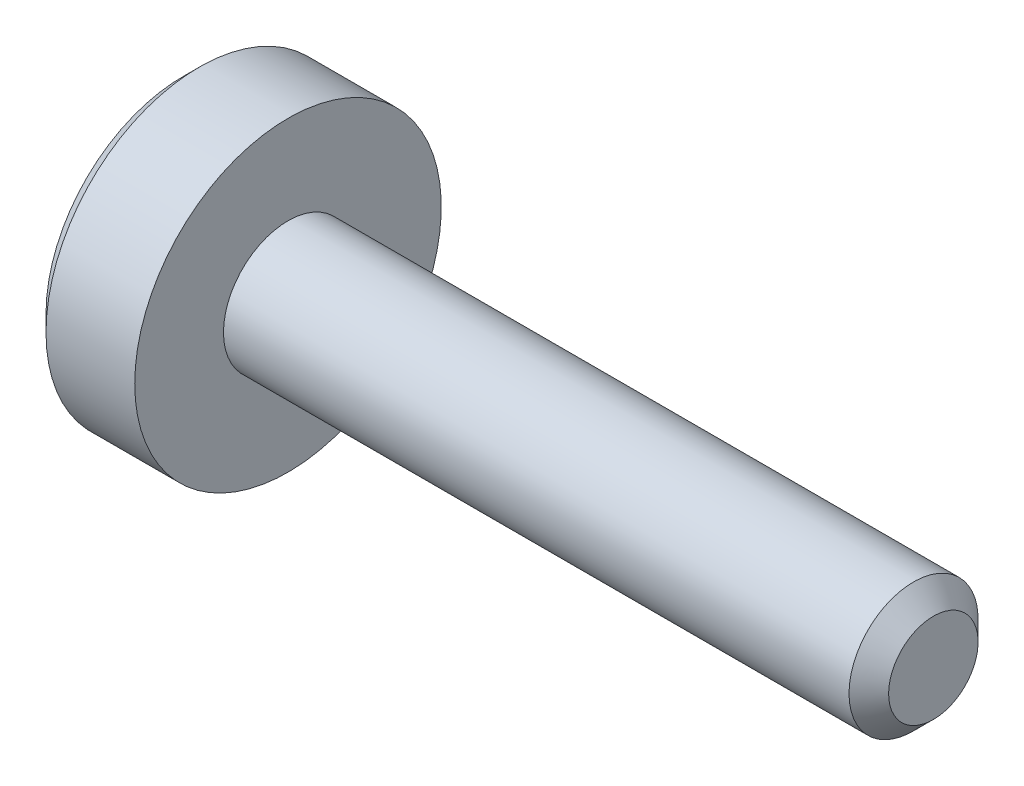
SolidWorks part; units mm, degrees
material "AISI 304"
ref_plane "正面" through (0, 0, 0) normal (0, 0, 1) x (1, 0, 0)
ref_plane "平面" through (0, 0, 0) normal (0, 1, 0) x (1, 0, 0)
ref_plane "右側面" through (0, 0, 0) normal (1, 0, 0) x (0, 0, -1)
ref_plane "Plane1" through (0, 0, 0) normal (0, 0, 1) x (1, 0, 0)
sketch "Sketch1" plane through (0, 0, 0) normal (0, 0, 1) x (1, 0, 0)
  line L0 (-1.3, 0) -> (-1.3, 1.7)
  line L1 (-1.3, 1.7) -> (-1.1, 1.9)
  line L2 (-1.1, 1.9) -> (0, 1.9)
  line L3 (0, 1.9) -> (0, 0.8)
  line L4 (0, 0.8) -> (7.7545, 0.8)
  line L5 (7.7545, 0.8) -> (8, 0.5545)
  line L6 (8, 0.5545) -> (8, 0)
  line L7 (8, 0) -> (-1.3, 0)
  line L8 (8, 0) -> (-1.3, 0) construction
  dimension "D1" = 0.8
revolve "Revolve1" add sketch "Sketch1" angle 360 about L8
cosmetic thread "Cosmetic Thread1"
ref_plane "Plane2" through (-1.3, 0, 0) normal (1, 0, 0) x (0, 0, -1)
sketch "Sketch2" plane through (-1.3, 0, 0) normal (1, 0, 0) x (0, 0, -1)
  line L0 (-0.65, -0.3753) -> (0, -0.7506)
  line L1 (0, -0.7506) -> (0.65, -0.3753)
  line L2 (0.65, -0.3753) -> (0.65, 0.3753)
  line L3 (0.65, 0.3753) -> (0, 0.7506)
  line L4 (0, 0.7506) -> (-0.65, 0.3753)
  line L5 (-0.65, 0.3753) -> (-0.65, -0.3753)
extrude "Cut-Extrude1" cut sketch "Sketch2" along normal blind 0.7
